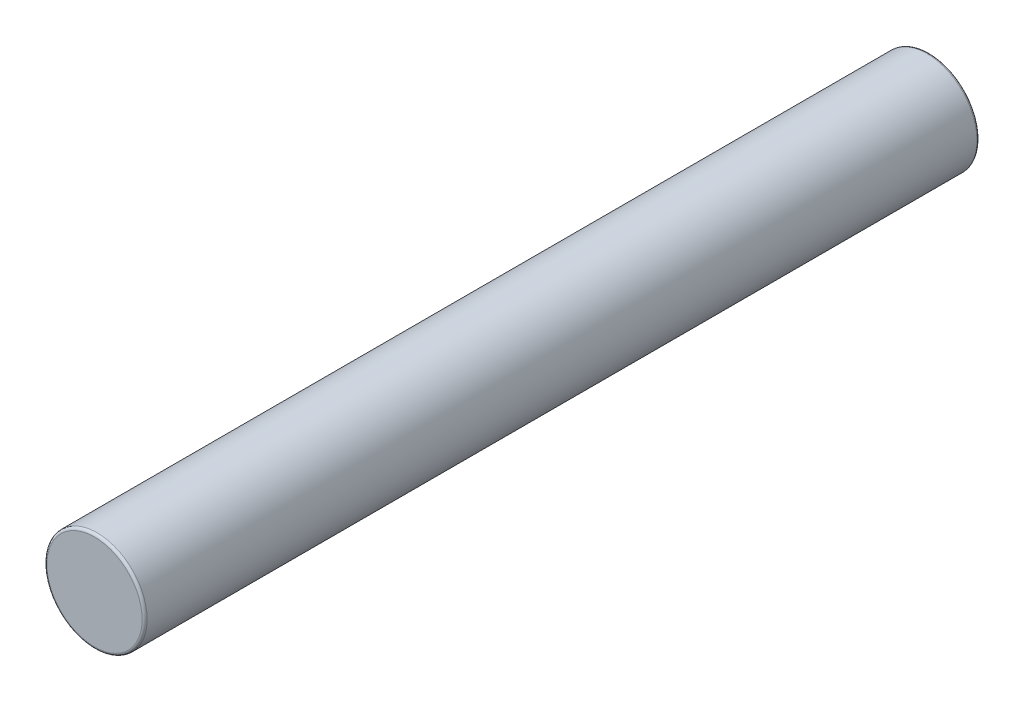
SolidWorks part; units mm, degrees
ref_plane "Front Plane" through (0, 0, 0) normal (0, 0, 1) x (1, 0, 0)
ref_plane "Top Plane" through (0, 0, 0) normal (0, 1, 0) x (1, 0, 0)
ref_plane "Right Plane" through (0, 0, 0) normal (1, 0, 0) x (0, 0, -1)
sketch "Sketch1" plane through (0, 0, 0) normal (0, 0, 1) x (1, 0, 0)
  circle A0 centre (0, 0) radius 1.5
  dimension "D1" = 3
extrude "Boss-Extrude1" add sketch "Sketch1" along normal blind 25
fillet "Fillet1" radius 0.075 2 edges at (1.5, 0, 0) (1.5, 0, 25)
